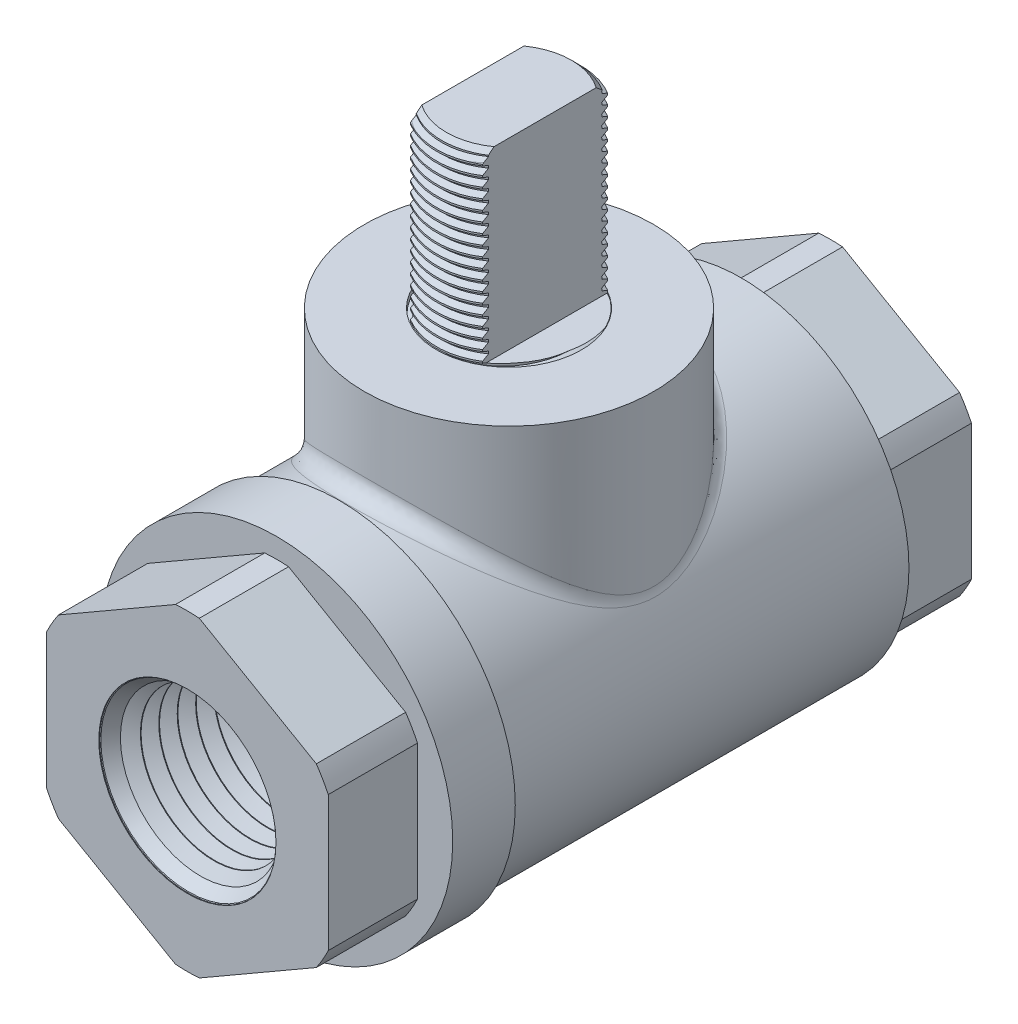
SolidWorks part; units mm, degrees
material "AISI 316 Stainless Steel Sheet (SS)"
ref_plane "Front" through (0, 0, 0) normal (0, 0, 1) x (1, 0, 0)
ref_plane "Top" through (0, 0, 0) normal (0, 1, 0) x (1, 0, 0)
ref_plane "Right" through (0, 0, 0) normal (1, 0, 0) x (0, 0, -1)
sketch "Sketch1" plane through (0, -2.9295, 125.5668) normal (1, 0, 0) x (0, 0, -1)
  line L0 (138.978, 2.9295) -> (138.978, 8.3761)
  line L1 (138.978, 8.3761) -> (139.6451, 9.6196) construction
  line L2 (139.6451, 9.6196) -> (140.3885, 8.4202) construction
  line L3 (140.3885, 8.4202) -> (141.0555, 9.6637) construction
  line L4 (141.0555, 9.6637) -> (141.7989, 8.4642) construction
  line L5 (140.4139, 8.4676) -> (141.0301, 9.6162)
  line L6 (141.0301, 9.6162) -> (141.0838, 9.6179)
  line L7 (141.0838, 9.6179) -> (141.7705, 8.51)
  line L8 (141.7705, 8.51) -> (141.8243, 8.5116)
  line L9 (138.978, 8.3761) -> (141.7989, 8.4642) construction
  line L10 (139.6451, 9.6196) -> (141.0555, 9.6637) construction
  line L11 (139.3116, 8.9978) -> (141.4272, 9.0639) construction
  line L12 (138.978, 2.9295) -> (125.5668, 2.9295) construction
  line L13 (141.8243, 8.5116) -> (142.4405, 9.6603)
  line L14 (139.0035, 8.4235) -> (139.6197, 9.5722)
  line L15 (139.6197, 9.5722) -> (139.6734, 9.5738)
  line L16 (139.6734, 9.5738) -> (140.3601, 8.4659)
  line L17 (140.3601, 8.4659) -> (140.4139, 8.4676)
  line L18 (139.3116, 8.9978) -> (138.978, 8.9874) construction
  line L19 (138.978, 8.9874) -> (138.978, 8.3761) construction
  line L20 (139.3116, -3.1388) -> (138.978, -3.1284) construction
  line L21 (139.0035, 8.4235) -> (138.978, 8.3761)
  line L22 (142.4405, 9.6603) -> (142.4943, 9.662)
  line L23 (142.4943, 9.662) -> (143.181, 8.554)
  line L24 (143.181, 8.554) -> (143.2347, 8.5557)
  line L25 (143.2347, 8.5557) -> (143.8509, 9.7044)
  line L26 (143.8509, 9.7044) -> (143.9047, 9.7061)
  line L27 (143.9047, 9.7061) -> (144.5914, 8.5981)
  line L28 (144.5914, 8.5981) -> (144.6452, 8.5998)
  line L29 (144.6452, 8.5998) -> (145.2613, 9.7485)
  line L30 (145.2613, 9.7485) -> (145.3151, 9.7502)
  line L31 (145.3151, 9.7502) -> (146.0018, 8.6422)
  line L32 (146.0018, 8.6422) -> (146.0556, 8.6439)
  line L33 (146.0556, 8.6439) -> (146.6718, 9.7926)
  line L34 (146.6718, 9.7926) -> (146.7255, 9.7942)
  line L35 (146.7255, 9.7942) -> (147.4122, 8.6863)
  line L36 (147.4122, 8.6863) -> (147.466, 8.6879)
  line L37 (147.466, 8.6879) -> (148.0822, 9.8366)
  line L38 (148.0822, 9.8366) -> (148.136, 9.8383)
  line L39 (148.136, 9.8383) -> (148.8227, 8.7303)
  line L40 (148.8227, 8.7303) -> (148.8764, 8.732)
  line L41 (148.8764, 8.732) -> (149.4926, 9.8807)
  line L42 (149.4926, 9.8807) -> (149.5464, 9.8824)
  line L43 (149.5464, 9.8824) -> (150.2331, 8.7744)
  line L44 (150.2331, 8.7744) -> (150.2869, 8.7761)
  line L45 (150.2869, 8.7761) -> (150.903, 9.9248)
  line L46 (150.903, 9.9248) -> (150.9568, 9.9265)
  line L47 (150.9568, 9.9265) -> (151.6435, 8.8185)
  line L48 (151.6435, 8.8185) -> (151.6973, 8.8202)
  line L49 (151.6973, 8.8202) -> (152.3135, 9.9689)
  line L50 (152.3135, 9.9689) -> (152.3672, 9.9706)
  line L51 (152.3672, 9.9706) -> (153.0539, 8.8626)
  line L52 (153.0539, 8.8626) -> (153.1077, 8.8643)
  line L53 (153.1077, 8.8643) -> (153.7239, 10.0129)
  line L54 (153.7239, 10.0129) -> (153.7776, 10.0146)
  line L55 (153.7776, 10.0146) -> (154.4644, 8.9067)
  line L56 (154.4644, 8.9067) -> (154.5181, 8.9083)
  line L57 (154.5181, 8.9083) -> (155.1343, 10.057)
  line L58 (155.1343, 10.057) -> (155.1881, 10.0587)
  line L59 (155.1881, 10.0587) -> (155.8748, 8.9507)
  line L60 (155.8748, 8.9507) -> (155.9285, 8.9524)
  line L61 (155.9285, 8.9524) -> (156.5447, 10.1011)
  line L62 (156.5447, 10.1011) -> (156.5985, 10.1028)
  line L63 (156.5985, 10.1028) -> (157.2852, 8.9948)
  line L64 (157.2852, 8.9948) -> (157.339, 8.9965)
  line L65 (157.339, 8.9965) -> (157.9551, 10.1452)
  line L66 (157.9551, 10.1452) -> (158.0089, 10.1469)
  line L67 (158.0089, 10.1469) -> (158.6956, 9.0389)
  line L68 (158.6956, 9.0389) -> (158.7494, 9.0406)
  line L69 (158.7494, 9.0406) -> (159.3656, 10.1893)
  line L70 (159.3656, 10.1893) -> (159.4193, 10.1909)
  line L71 (159.4193, 10.1909) -> (160.106, 9.083)
  line L72 (160.106, 9.083) -> (160.1598, 9.0847)
  line L73 (138.978, 2.9295) -> (160.1598, 2.9295)
  line L74 (160.1598, 2.9295) -> (160.1598, 9.0847)
  line L75 (139.6465, 9.573) -> (139.6451, 9.6196) construction
  line L76 (141.4272, 9.0639) -> (149.1888, 9.3065) construction
  line L77 (149.1888, 9.3065) -> (149.1888, 2.9295) construction
  line L78 (149.1888, 9.3065) -> (150.9668, 9.3621) construction
  line L79 (150.9668, 9.3621) -> (150.9668, 2.9295) construction
  line L84 (149.1888, 8.7418) -> (150.9668, 8.7974) construction
  line L85 (138.978, 5.6528) -> (125.5668, 5.6528) construction
  line L86 (125.5668, 5.6528) -> (125.5668, 2.9295) construction
  dimension "D1" = 60
  dimension "E0" = 12.1158
  dimension "Thread Pitch" = 1.4111
  dimension "D4" = 3.58
  dimension "D3" = 0.0538
  dimension "L2 Thread Engagement" = 10.2108
  dimension "l Thread Length" = 11.9888
  dimension "Body Length" = 50.8
revolve "Revolve1" add sketch "Sketch1" angle 360 about L12
sketch "Sketch6" plane through (0, 0, 0) normal (1, 0, 0) x (0, 0, -1)
  line L0 (25.4, 0) -> (25.4, 6.9973)
  line L1 (25.4, 6.9973) -> (34.593, 7.2846)
  line L2 (34.593, 7.2846) -> (34.593, 0)
  line L3 (34.593, 0) -> (25.4, 0)
  line L4 (25.4, 6.4326) -> (25.4, 0) construction
  line L5 (13.4112, 0) -> (34.593, 0) construction
  line L6 (34.593, 0) -> (34.593, 6.1551) construction
  line L7 (26.7466, 7.0394) -> (26.8004, 7.041) construction
revolve "Cut-Revolve3" cut sketch "Sketch6" angle 360 about L3
sketch "Sketch7" plane through (0, 0, 0) normal (1, 0, 0) x (0, 0, -1)
  line L0 (23.622, 5.8123) -> (25.4, 6.9973)
  line L1 (25.4, 6.9973) -> (25.4, 5.8679)
  line L2 (25.4, 5.8679) -> (23.622, 5.8123)
  line L3 (25.4, 6.4326) -> (25.4, 0) construction
  line L4 (14.0528, 6.6427) -> (14.1066, 6.6443) construction
  line L5 (23.622, 5.8123) -> (25.4, 5.8679) construction
  line L6 (13.4112, 0) -> (23.622, 0) construction
  line L7 (23.622, 0) -> (23.622, 5.8123) construction
  line L8 (13.4112, 0) -> (13.4112, 5.4466) construction
  line L9 (0, 0) -> (13.4112, 0)
  line L10 (0, 0) -> (0, 5.334)
  line L11 (0, 5.334) -> (13.2986, 5.334)
  line L12 (13.4112, 0) -> (13.4112, 5.4466)
  line L13 (13.4112, 5.4466) -> (13.2986, 5.334)
  dimension "D1" = 45
  dimension "Min ID" = 10.668
revolve "Revolve3" add sketch "Sketch7" angle 360 about L6
mirror "Mirror2" about plane through (0, 0, 0) normal (0, 0, 1) of bodies 114
sketch "Sketch8" plane through (0, 0, 25.4) normal (0, 0, 1) x (1, 0, 0)
  line L1 (0, 12.8463) -> (-11.1252, 6.4231)
  line L2 (-11.1252, 6.4231) -> (-11.1252, -6.4231)
  line L3 (-11.1252, -6.4231) -> (0, -12.8463)
  line L4 (0, -12.8463) -> (11.1252, -6.4231)
  line L5 (11.1252, -6.4231) -> (11.1252, 6.4231)
  line L6 (11.1252, 6.4231) -> (0, 12.8463)
  circle A0 centre (0, 0) radius 11.1252 construction
  dimension "Body Hex" = 22.2504
extrude "Extrude1" add sketch "Sketch8" against normal up to surface (50.8 mm away) separate body
sketch "Sketch9" plane through (0, 0, 0) normal (1, 0, 0) x (0, 0, -1)
  line L0 (-18.3501, 6.4231) -> (-18.3501, 13.9065)
  line L1 (-18.3501, 13.9065) -> (-13.4112, 13.9065)
  line L2 (-13.4112, 13.9065) -> (-13.4112, 13.5149)
  line L3 (-13.4112, 13.5149) -> (-13.1343, 13.2379)
  line L4 (-13.1343, 13.2379) -> (18.3501, 13.2379)
  line L5 (18.3501, 13.2379) -> (18.3501, 6.4231)
  line L6 (18.3501, 6.4231) -> (-18.3501, 6.4231)
  line L7 (25.4, 6.4231) -> (-25.4, 6.4231) construction
  line L8 (0, 0) -> (0, 6.4231) construction
  line L9 (13.4112, 0) -> (13.4112, 5.4466) construction
  line L10 (0, 0) -> (-18.3501, 0) construction
  line L11 (-18.3501, 0) -> (-18.3501, 6.4231) construction
  line L12 (-13.1343, 13.2379) -> (-13.1343, 12.8463) construction
  line L13 (25.4, 12.8463) -> (-25.4, 12.8463) construction
  line L14 (25.4, 6.4326) -> (25.4, 13.2379) construction
  line L15 (25.4, 13.2379) -> (18.3501, 13.2379) construction
  dimension "D1" = 4.9389
  dimension "D2" = 27.813
  dimension "D3" = 135
  dimension "D4" = 4.9389
revolve "Revolve4" add sketch "Sketch9" angle 360 about L10
sketch "Sketch10" plane through (0, 0, 0) normal (1, 0, 0) x (0, 0, -1)
  line L0 (0, 1.27) -> (0, 19.5625)
  line L1 (5.7023, 20.3499) -> (5.7277, 20.3499) construction
  line L2 (11.43, 20.3499) -> (11.43, 1.27)
  line L3 (11.43, 1.27) -> (0, 1.27)
  line L4 (0, 0) -> (0, 1.27) construction
  line L5 (-12.7, 15.5239) -> (-12.7, 20.6039) construction
  line L6 (-12.7, 20.6039) -> (12.7, 20.6039) construction
  line L7 (12.7, 20.6039) -> (55.5083, 40.5658) construction
  line L8 (-12.7, 15.5239) -> (-15.875, 15.5239) construction
  line L9 (-15.875, 15.5239) -> (-15.875, 23.7789) construction
  line L10 (-15.875, 23.7789) -> (11.9961, 23.7789) construction
  line L11 (11.9961, 23.7789) -> (55.5083, 44.069) construction
  line L12 (55.5083, 44.069) -> (55.5083, 40.5658) construction
  line L13 (18.3501, 13.2379) -> (-13.1343, 13.2379) construction
  line L14 (55.5083, 45.974) -> (55.5083, 38.6608) construction
  line L15 (55.5083, 38.6608) -> (101.6, 38.6608) construction
  line L16 (101.6, 38.6608) -> (101.6, 45.974) construction
  line L17 (101.6, 45.974) -> (55.5083, 45.974) construction
  line L18 (-1.9394, 23.7789) -> (-1.9394, 20.6039) construction
  line L19 (33.7522, 33.924) -> (35.094, 31.0464) construction
  line L20 (-11.43, 20.3499) -> (-11.43, 1.27) construction
  line L22 (55.5083, 38.6608) -> (55.5083, 4.3225) construction
  line L23 (18.3501, 13.2379) -> (-13.1343, 13.2379) construction
  line L26 (5.7023, 20.3499) -> (5.7023, 34.8279)
  line L27 (5.7023, 34.8279) -> (0, 34.8279)
  line L28 (5.7023, 20.3499) -> (5.7023, 19.5879)
  line L29 (5.7023, 19.5879) -> (0, 19.5879)
  line L30 (0, 19.5625) -> (5.7277, 19.5625)
  line L31 (5.7277, 19.5625) -> (5.7277, 20.3499)
  line L32 (5.7277, 20.3499) -> (11.43, 20.3499)
  line L33 (0, 19.5625) -> (0, 19.5879) construction
  line L34 (0, 19.5879) -> (0, 34.8279)
  line L35 (-5.7023, 20.3499) -> (-5.7023, 34.8279) construction
  line L36 (5.7277, 19.5625) -> (5.7277, 4.3225) construction
  line L37 (5.7277, 4.3225) -> (55.5083, 4.3225) construction
  point P26 (55.5083, 42.3174)
  dimension "Handle Height" = 45.974
  dimension "Handle Length" = 101.6
  dimension "D3" = 22.86
  dimension "D5" = 25.4229
  dimension "D6" = 3.175
  dimension "D7" = 1.27
  dimension "D8" = 0.254
  dimension "D9" = 1.27
  dimension "D11" = 0.0254
  dimension "D12" = 0.0254
  dimension "D13" = 15.24
  dimension "D14" = 0.762
  dimension "D2" = 1.905
  dimension "D4" = 155
  dimension "D10" = 11.4046
  dimension "D15" = 7.112
  dimension "D16" = 8.255
  dimension "D17" = 1.27
revolve "Revolve5" add sketch "Sketch10" angle 360 about L4
chamfer "Chamfer1" distance 0.762 angle 45 1 edges at (0, 34.8279, -5.7023)
fillet "Fillet5" radius 1.27 1 edges at (1.6403, 13.1359, 11.3117)
sketch "Sketch20" plane through (0, 0, 0) normal (1, 0, 0) x (0, 0, -1)
  line L0 (5.7023, 34.8279) -> (-5.7023, 34.8279) construction
  line L1 (-5.7023, 34.8279) -> (-5.7023, 34.0342) construction
  line L2 (-5.7023, 34.0342) -> (5.7023, 34.8279) construction
  line L3 (5.7023, 34.8279) -> (5.7092, 34.7289) construction
  line L4 (5.7092, 34.7289) -> (5.7574, 34.0361)
  line L5 (5.7574, 34.0361) -> (5.3116, 34.2537)
  line L6 (5.3116, 34.2537) -> (5.2978, 34.4517)
  line L7 (5.2978, 34.4517) -> (5.7092, 34.7289)
  line L8 (5.3047, 34.3527) -> (5.7333, 34.3825) construction
  line L9 (5.7023, 34.8279) -> (5.7023, 34.3804) construction
  line L10 (5.7023, 34.3804) -> (-5.7023, 33.5866) construction
  line L11 (-5.7023, 33.5866) -> (-5.7023, 34.0342) construction
  line L12 (-0.0588, 34.8279) -> (0.0588, 33.139) construction
  line L13 (-5.7023, 20.3499) -> (-5.7023, 34.8279) construction
  line L14 (5.7023, 20.3499) -> (5.7023, 34.8279) construction
  line L15 (5.7023, 34.8279) -> (0, 34.8279) construction
  point P13 (0, 33.9835)
  dimension "D1" = 0.0992
  dimension "D2" = 0.1984
  dimension "D3" = 0.7937
  dimension "D4" = 60
  dimension "D5" = 0.7937
revolve "Cut-Revolve6" cut sketch "Sketch20" angle 360 about L12
pattern_linear "LPattern1" count 2 spacing 0.7937 along (0, 1, 0) count 19 spacing 0.7937 along (0, -1, 0) of "Cut-Revolve6"
sketch "Sketch26" plane through (0, 19.5625, 0) normal (0, 1, 0) x (-1, 0, 0)
  circle A1 centre (0, 0) radius 5.7277
  circle A2 centre (0, 0) radius 5.7277
  dimension "D1" = 0
extrude "Extrude8" add sketch "Sketch26" along normal blind 0.127
sketch "Sketch16" plane through (0, 0, 0) normal (1, 0, 0) x (0, 0, -1)
  line L0 (-25.4, 6.4231) -> (-25.4, 12.8463) construction
  line L1 (25.4, 12.8463) -> (18.3501, 12.8463)
  line L2 (25.4, 12.8463) -> (25.4, 12.3383)
  line L3 (25.4, 12.3383) -> (18.3501, 12.3383)
  line L4 (18.3501, 12.8463) -> (18.3501, 12.3383)
  line L5 (-25.4, 12.8463) -> (-18.3501, 12.8463)
  line L6 (-25.4, 12.8463) -> (-25.4, 12.3383)
  line L7 (-25.4, 12.3383) -> (-18.3501, 12.3383)
  line L8 (-18.3501, 12.8463) -> (-18.3501, 12.3383)
  line L9 (25.4, 12.8463) -> (25.4, 6.4231) construction
  line L10 (18.3501, -13.2379) -> (18.3501, 13.2379) construction
  line L11 (-18.3501, 13.9065) -> (-18.3501, -13.9065) construction
  line L12 (-18.3501, 12.8463) -> (-25.4, 12.8463) construction
  line L13 (0, 0) -> (-25.4, 0) construction
  line L14 (-25.4, 0) -> (-25.4, 12.3383) construction
  dimension "D1" = 0.508
revolve "Cut-Revolve5" cut sketch "Sketch16" angle 360 about L13
combine bodies "Combine1" operation type subtract main body 126 bodies to subtract 115
ref_plane "Plane2" through (0, 34.8279, 0) normal (0, 1, 0) x (-1, 0, 0)
sketch "Sketch27" plane through (0, 34.8279, 0) normal (0, 1, 0) x (-1, 0, 0)
  line L0 (-2.8511, -5.7023) -> (2.8511, 5.7023) construction
  line L1 (-2.8511, 5.7023) -> (2.8511, 5.7023)
  line L2 (-2.8511, 5.7023) -> (-2.8511, -5.7023)
  line L3 (-2.8511, -5.7023) -> (2.8511, -5.7023)
  line L4 (2.8511, 5.7023) -> (2.8511, -5.7023)
  dimension "D1" = 5.7023
extrude "Cut-Extrude3" cut sketch "Sketch27" against normal up to surface (14.478 mm away) flip side to cut up to face at (0, 20.3499, -5.7277)
equation "\"D2@Sketch1\"=\"Thread Pitch@Sketch1\"*.033"
equation "\"D2@Sketch9\"=\"Body Hex@Sketch8\"*1.25"
equation "\"D1@Sketch9\" = \"Thread Pitch@Sketch1\"*3.5"
equation "\"D4@Sketch9\"=\"D1@Sketch9\""
equation "\"D2@LPattern1\"=\"D13@Sketch10\"/\"D3@Sketch20\""
equation "\"D1@Sketch27\"=\"D10@Sketch10\"/2"
